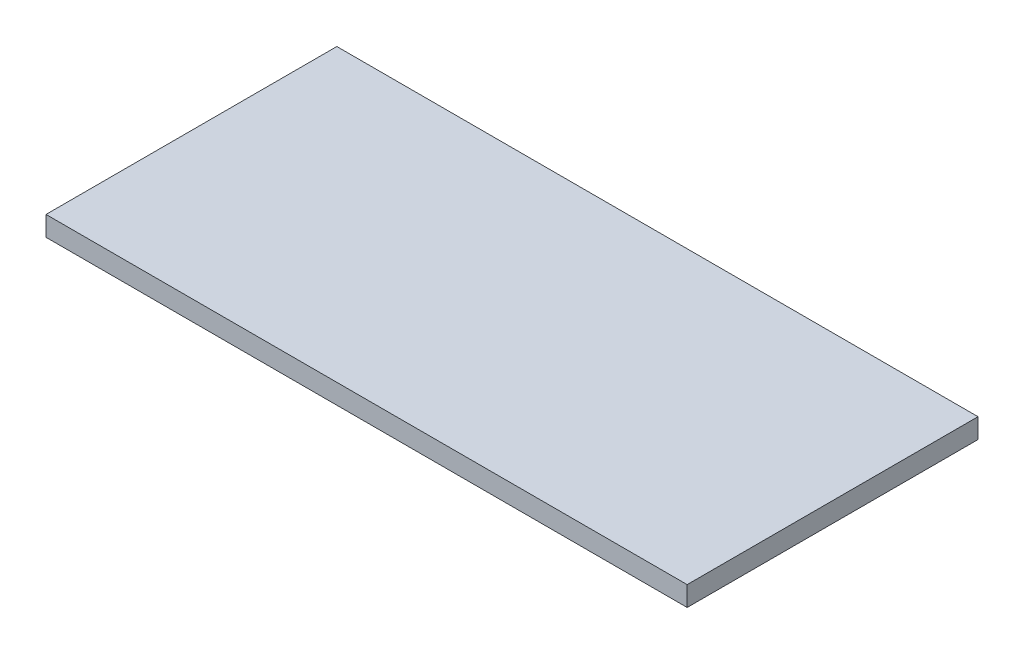
SolidWorks part; units mm, degrees
ref_plane "Front Plane" through (0, 0, 0) normal (0, 0, 1) x (1, 0, 0)
ref_plane "Top Plane" through (0, 0, 0) normal (0, 1, 0) x (1, 0, 0)
ref_plane "Right Plane" through (0, 0, 0) normal (1, 0, 0) x (0, 0, -1)
sketch "Sketch1" plane through (0, 0, 0) normal (0, 1, 0) x (1, 0, 0)
  line L1 (-48.5, 22) -> (48.5, 22)
  line L2 (-48.5, 22) -> (-48.5, -22)
  line L3 (-48.5, -22) -> (48.5, -22)
  line L4 (48.5, 22) -> (48.5, -22)
  point P4 (0, -22)
  point P6 (48.5, 0)
  dimension "D1" = 44
  dimension "D2" = 97
extrude "Boss-Extrude1" add sketch "Sketch1" along normal blind 3
